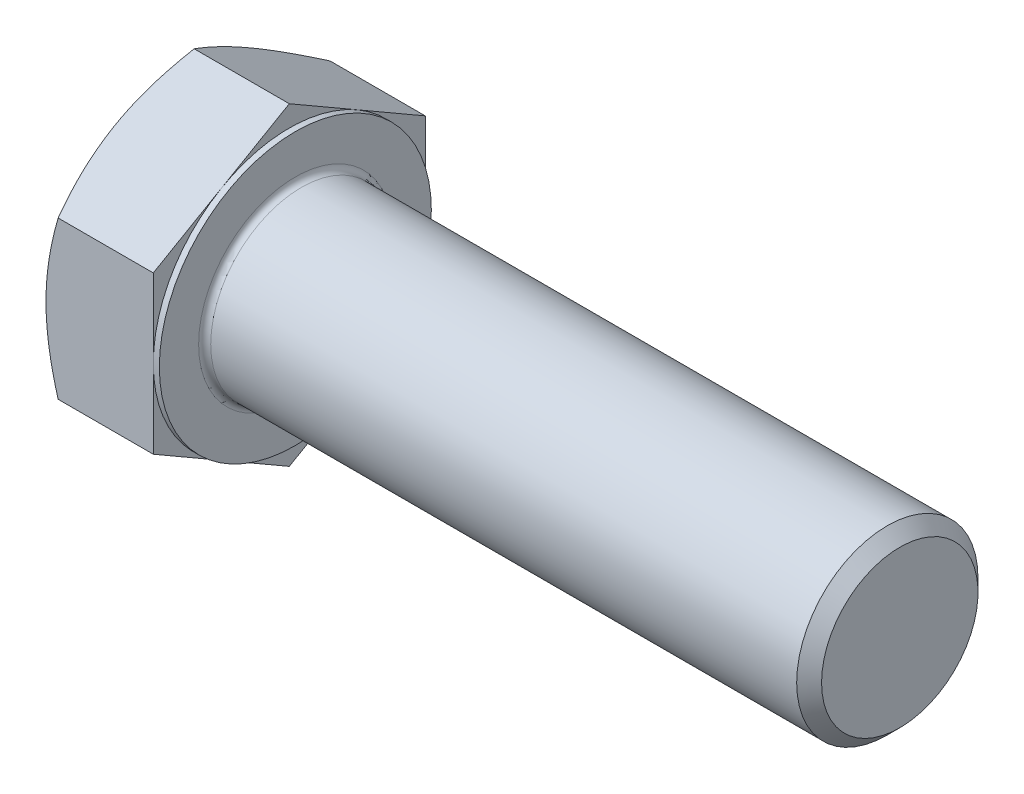
SolidWorks part; units mm, degrees
ref_plane "Front Plane" through (0, 0, 0) normal (0, 0, 1) x (1, 0, 0)
ref_plane "Top Plane" through (0, 0, 0) normal (0, 1, 0) x (1, 0, 0)
ref_plane "Right Plane" through (0, 0, 0) normal (1, 0, 0) x (0, 0, -1)
sketch "BaseHeadSke" plane through (0, 0, 0) normal (1, 0, 0) x (0, 0, -1)
  line L1 (18, 10.3923) -> (0, 20.7846)
  line L2 (0, 20.7846) -> (-18, 10.3923)
  line L3 (-18, 10.3923) -> (-18, -10.3923)
  line L4 (-18, -10.3923) -> (0, -20.7846)
  line L5 (0, -20.7846) -> (18, -10.3923)
  line L6 (18, -10.3923) -> (18, 10.3923)
  circle A0 centre (0, 0) radius 18 construction
extrude "BaseHead" add sketch "BaseHeadSke" along normal blind 15
sketch "BodySke" plane through (0, 0, 0) normal (0, 0, 1) x (1, 0, 0)
  line L0 (0, 0) -> (95, 0)
  line L1 (95, 0) -> (95, 10.352)
  line L2 (95, 10.352) -> (93.352, 12)
  line L3 (93.352, 12) -> (0, 12)
  line L4 (0, 12) -> (0, 0)
  line L5 (15, 10.3923) -> (15, -10.3923) construction
  line L6 (0, 0) -> (159.3976, 0) construction
  line L7 (15, -84.3176) -> (15, 77.7215) construction
  line L8 (92, -21.5941) -> (92, 39.2994) construction
  dimension "Ang" = 45
  dimension "Thread_length" = 18
  dimension "Advance" = 1
revolve "BaseBody" add sketch "BodySke" angle 360 about L6
cosmetic thread "ThreadCosmetic" [suppressed] parameters "Thread_length"=18, "Thread_minor"=4.891
sketch "HeadChamferSke" plane through (0, 0, 0) normal (0, 0, 1) x (1, 0, 0)
  line L0 (1.6077, 20.7846) -> (0, 20.7846)
  line L1 (0, 20.7846) -> (0, 18)
  line L2 (0, 18) -> (1.6077, 20.7846)
  line L3 (0, 0) -> (120.9185, 0) construction
  dimension "D1" = 30
  dimension "Head_chamfer" = 10
revolve "HeadChamfer" cut sketch "HeadChamferSke" angle 360 about L3
sketch "BearingFaceSke" plane through (0, 0, 0) normal (0, 0, 1) x (1, 0, 0)
  line L0 (0, 0) -> (129.6443, 0) construction
  line L1 (14.2, 20.7846) -> (15, 20.7846)
  line L2 (14.2, 20.7846) -> (14.2, 18)
  line L3 (14.2, 18) -> (15, 18)
  line L4 (15, 20.7846) -> (15, 18)
  dimension "D1" = 10
revolve "BearingFace" cut sketch "BearingFaceSke" angle 360 about L0
fillet "Fillet" radius 0.8 1 edges at (15, 0, 12)
sketch "ThdSchSke" plane through (0, 0, 0) normal (0, 0, 1) x (1, 0, 0)
  line L0 (91.0485, 13.9029) -> (91.0485, 12)
  line L1 (91.0485, 12) -> (92, 10.352)
  line L2 (92, 10.352) -> (92.9515, 12)
  line L3 (92.9515, 12) -> (92.9515, 13.9029)
  line L4 (92.9515, 13.9029) -> (91.0485, 13.9029)
  line L6 (0, 0) -> (141.9934, 0) construction
  line L7 (95, -10.352) -> (95, 10.352) construction
  dimension "D2" = 4.891
  dimension "D3" = 6
  dimension "Advance" = 1
revolve "ThreadSchematic" [suppressed] cut sketch "ThdSchSke" angle 360 about L6
pattern_linear "ThdSchPat" [suppressed] count 17 spacing 1 along (1, 0, 0)
equation "\"Thread_minor@ThreadCosmetic\" = \"Minor_dia@BodySke\""
equation "\"Thread_length@ThreadCosmetic\" = \"Thread_length@BodySke\""
equation "\"Head_chamfer@HeadChamferSke\" = \"Width_flats@BaseHeadSke\""
equation "\"D1@BearingFaceSke\" = \"Width_flats@BaseHeadSke\""
equation "\"D2@ThdSchSke\" = \"Minor_dia@BodySke\""
equation "\"D3@ThdSchSke\" = \"Diameter@BodySke\""
equation "\"Advance@ThdSchSke\" = \"Advance@BodySke\""
equation "\"D3@ThdSchPat\" = \"Advance@BodySke\""
equation "\"D1@ThdSchPat\" =  int( \"Thread_length@BodySke\"/\"Advance@BodySke\" )-1"
